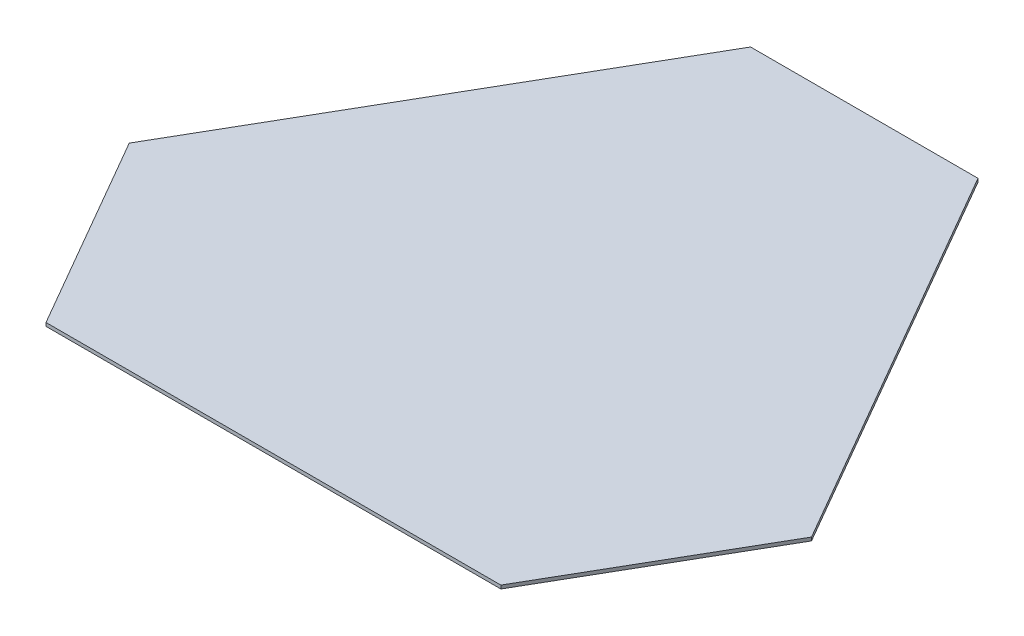
SolidWorks part; units mm, degrees
material "AISI 1020"
ref_plane "Front Plane" through (0, 0, 0) normal (0, 0, 1) x (1, 0, 0)
ref_plane "Top Plane" through (0, 0, 0) normal (0, 1, 0) x (1, 0, 0)
ref_plane "Right Plane" through (0, 0, 0) normal (1, 0, 0) x (0, 0, -1)
sketch "Sketch2" plane through (0, 0, 0) normal (0, 1, 0) x (1, 0, 0)
  line L0 (-100, 288.6751) -> (100, 288.6751)
  line L1 (100, 288.6751) -> (300, -57.735)
  line L2 (300, -57.735) -> (200, -230.9401)
  line L3 (200, -230.9401) -> (-200, -230.9401)
  line L4 (-200, -230.9401) -> (-300, -57.735)
  line L5 (-300, -57.735) -> (-100, 288.6751)
  line L6 (-250, -144.3376) -> (200, 115.4701)
  point P3 (0, 288.6751)
  point P11 (0, 0)
  point P13 (0, 0)
  dimension "D1" = 200
  dimension "D2" = 400
  dimension "D3" = 400
  dimension "D4" = 200
  dimension "D5" = 400
  dimension "D6" = 200
  dimension "D7" = 120
  dimension "D8" = 120
  dimension "D9" = 519.6152
  dimension "D10" = 0
  dimension "D11" = 90
extrude "Boss-Extrude1" add sketch "Sketch2" along normal blind 3 contours L4 L6 L1 L0 L5 | L6 L4 L3 L2 L1
